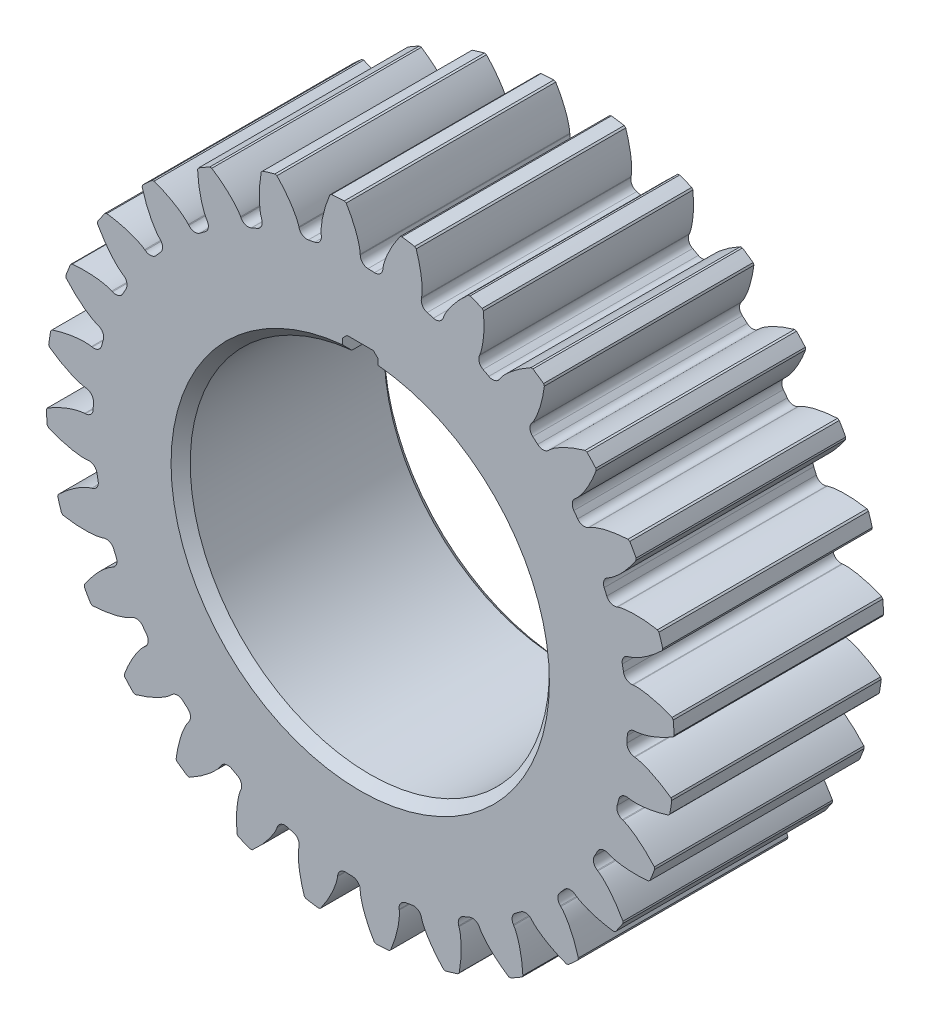
SolidWorks part; units mm, degrees
material "1.6587 (18CrNiMo7-6)"
ref_plane "Front Plane" through (0, 0, 0) normal (0, 0, 1) x (1, 0, 0)
ref_plane "Top Plane" through (0, 0, 0) normal (0, 1, 0) x (1, 0, 0)
ref_plane "Right Plane" through (0, 0, 0) normal (1, 0, 0) x (0, 0, -1)
sketch "Sketch1" plane through (0, 0, 0) normal (0, 0, 1) x (1, 0, 0)
  circle A0 centre (0, 0) radius 49 construction
  circle A1 centre (0, 0) radius 44.625
  dimension "D1" = 98
  dimension "D2" = 4.375
extrude "Boss-Extrude1" add sketch "Sketch1" along normal blind 35
sketch "Sketch2" plane through (0, 0, 0) normal (0, 0, 1) x (1, 0, 0)
  line L0 (46.045, 0) -> (45.9188, -0.0016)
  line L1 (0, 0) -> (48.9946, 0.7303) construction
  line L2 (0, 0) -> (60.4106, 4.2966) construction
  line L3 (45.5815, 6.5168) -> (45.4564, 6.5006)
  circle A0 centre (0, 0) radius 49 construction
  arc A1 (44.6063, -1.293) -> (43.9743, 7.5931) centre (0, 0) ccw
  arc A2 (52.4429, 2.4478) -> (52.2614, 4.9992) centre (0, 0) ccw
  arc A3 (45.9188, -0.0016) -> (44.6063, -1.293) centre (45.9357, -1.3315) ccw
  arc A4 (45.4564, 6.5006) -> (43.9743, 7.5931) centre (45.2849, 7.8194) cw
  circle A5 centre (0, 0) radius 52.5 construction
  circle A6 centre (0, 0) radius 44.625 construction
  spline S0 degree 4 poles (46.045, 0) (46.0573, 0.0002) (46.0916, 0.0011) (46.1566, 0.0047) (46.2625, 0.0134) (46.3972, 0.0283) (46.5712, 0.0522) (46.7757, 0.0863) (46.9999, 0.1298) (47.2433, 0.1837) (47.4856, 0.2433) (47.7266, 0.3082) (47.9661, 0.3778) (48.2554, 0.4677) (48.6012, 0.5836) (49.0036, 0.7307) (49.4576, 0.9111) (49.9177, 1.1095) (50.3682, 1.3168) (50.8205, 1.5398) (51.256, 1.7652) (51.7053, 2.0132) (52.1183, 2.2493) (52.5773, 2.529) (52.9466, 2.7592) (53.4295, 3.079) (53.7134, 3.2727) (54.0441, 3.5049) (54.1901, 3.6109) (54.2801, 3.6762) knots 0 0 0 0 0 0.005377 0.015084 0.028532 0.04661 0.064855 0.092111 0.119476 0.146842 0.174209 0.201575 0.228941 0.256307 0.307035 0.361767 0.4165 0.471232 0.525964 0.580697 0.635429 0.690161 0.744894 0.799626 0.854358 0.909091 0.954545 1 1 1 1 1 construction
  spline S1 degree 4 poles (46.045, 0) (46.0573, 0.0002) (46.0916, 0.0011) (46.1566, 0.0047) (46.2625, 0.0134) (46.3972, 0.0283) (46.5712, 0.0522) (46.7757, 0.0863) (46.9999, 0.1298) (47.2433, 0.1837) (47.4856, 0.2433) (47.7266, 0.3082) (47.9661, 0.3778) (48.2554, 0.4677) (48.6012, 0.5836) (49.0036, 0.7307) (49.4576, 0.9111) (49.9177, 1.1095) (50.3682, 1.3168) (50.8205, 1.5398) (51.256, 1.7652) (51.7053, 2.0132) (52.0382, 2.2035) (52.2867, 2.3527) (52.4189, 2.4331) (52.4429, 2.4478) knots 0 0 0 0 0 0.005377 0.015084 0.028532 0.04661 0.064855 0.092111 0.119476 0.146842 0.174209 0.201575 0.228941 0.256307 0.307035 0.361767 0.4165 0.471232 0.525964 0.580697 0.635429 0.690161 0.744894 0.757146 0.757146 0.757146 0.757146 0.757146
  spline S2 degree 4 poles (45.5815, 6.5168) (45.5937, 6.5184) (45.6278, 6.5224) (45.6926, 6.5279) (45.7987, 6.5344) (45.9342, 6.5386) (46.1097, 6.5396) (46.317, 6.5349) (46.5452, 6.5235) (46.7938, 6.5046) (47.042, 6.4798) (47.2898, 6.4497) (47.5367, 6.4148) (47.8358, 6.3666) (48.1946, 6.3009) (48.6137, 6.2122) (49.0887, 6.0979) (49.5723, 5.9666) (50.0475, 5.8252) (50.5268, 5.6684) (50.9899, 5.5069) (51.4697, 5.325) (51.8262, 5.1838) (52.0934, 5.0712) (52.2356, 5.0103) (52.2614, 4.9992) knots 0 0 0 0 0 0.005377 0.015084 0.028532 0.04661 0.064855 0.092111 0.119476 0.146842 0.174209 0.201575 0.228941 0.256307 0.307035 0.361767 0.4165 0.471232 0.525964 0.580697 0.635429 0.690161 0.744894 0.757146 0.757146 0.757146 0.757146 0.757146
  dimension "D1" = 98
  dimension "D4" = 2.66
  dimension "D5" = 3.214
  dimension "D2" = 4.375
  dimension "D3" = 3.5
extrude "Boss-Extrude2" add sketch "Sketch2" along normal blind 35
chamfer "Chamfer1" distance 0.2 2 edges at (52.4429, 2.4478, 17.5) (52.2614, 4.9992, 17.5)
pattern_circular "CirPattern1" count 28 over 360 about axis through (0, 0, 35) along (0, 0, -1) of "Chamfer1", "Boss-Extrude2"
sketch "Sketch3" plane through (0, 0, 35) normal (0, 0, 1) x (1, 0, 0)
  line L0 (0, 0) -> (0, 33.2) construction
  line L1 (3, 29.8496) -> (3, 33.2)
  line L2 (-3, 29.8496) -> (-3, 33.2)
  line L4 (3, 33.2) -> (-3, 33.2)
  line L5 (3, 0) -> (3, 33.2) construction
  line L6 (-3, 0) -> (-3, 33.2) construction
  arc A0 (-3, 29.8496) -> (3, 29.8496) centre (0, 0) ccw
  dimension "D1" = 60
  dimension "D2" = 33.2
  dimension "D3" = 3
  dimension "D4" = 3
extrude "Cut-Extrude1" cut sketch "Sketch3" against normal blind 35
chamfer "Chamfer2" distance 1.6 1 edges at (0, -30, 35)
chamfer "Chamfer3" distance 1 1 edges at (0, -30, 0)
chamfer "Chamfer4" distance 0.8 2 edges at (3, 33.2, 17.5) (-3, 33.2, 17.5)
